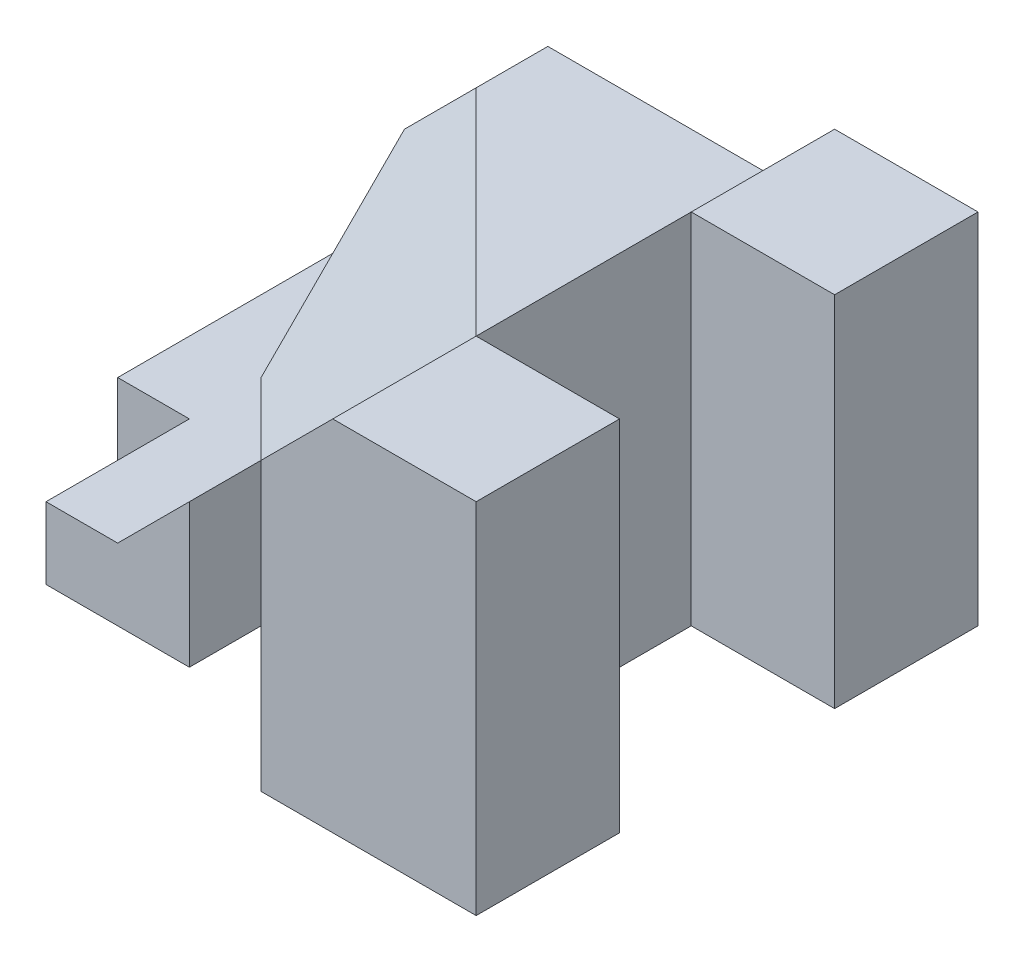
SolidWorks part; units mm, degrees
ref_plane "Front Plane" through (0, 0, 0) normal (0, 0, 1) x (1, 0, 0)
ref_plane "Top Plane" through (0, 0, 0) normal (0, 1, 0) x (1, 0, 0)
ref_plane "Right Plane" through (0, 0, 0) normal (1, 0, 0) x (0, 0, -1)
sketch "Sketch1" plane through (0, 0, 0) normal (0, 1, 0) x (1, 0, 0)
  line L0 (0, 0) -> (0, -2)
  line L1 (0, -2) -> (-2, -2)
  line L2 (-2, -2) -> (-2, -5)
  line L3 (-2, -5) -> (0, -5)
  line L4 (0, -5) -> (0, -7)
  line L5 (0, -7) -> (-3, -7)
  line L6 (-3, -7) -> (-3, -5)
  line L7 (-3, -5) -> (-5, -5)
  line L8 (-5, -5) -> (-5, -6)
  line L9 (-5, -6) -> (-7, -6)
  line L10 (-7, -6) -> (-7, -4)
  line L11 (-7, -4) -> (-8, -4)
  line L12 (-8, -4) -> (-8, 0)
  line L13 (-8, 0) -> (0, 0)
  dimension "D1" = 2
  dimension "D2" = 2
  dimension "D3" = 3
  dimension "D4" = 2
  dimension "D5" = 3
  dimension "D6" = 2
  dimension "D7" = 2
  dimension "D8" = 1
  dimension "D9" = 2
  dimension "D10" = 1
  dimension "D11" = 4
extrude "Boss-Extrude1" add sketch "Sketch1" along normal blind 5
sketch "Sketch2" plane through (0, 0, 6) normal (0, 0, 1) x (1, 0, 0)
  line L0 (-8, 1) -> (-6, 1)
  line L1 (-8, 5) -> (-8, 0) construction
  line L2 (-6, 1) -> (-2, 5)
  line L3 (-5, 5) -> (-3, 5) construction
  line L4 (-2, 5) -> (-8, 5)
  line L5 (-8, 5) -> (-8, 1)
  dimension "D1" = 4
  dimension "D2" = 2
  dimension "D3" = 6
extrude "Cut-Extrude1" cut sketch "Sketch2" against normal blind 2 and the other way blind 5
sketch "Sketch3" plane through (0, 0, 4) normal (0, 0, 1) x (1, 0, 0)
  line L0 (-2, 5) -> (-3, 5)
  line L1 (-8, 5) -> (-2, 5) construction
  line L2 (-3, 4) -> (-8, 4)
  line L3 (-6, 1) -> (-2, 5) construction
  line L4 (-3, 4) -> (-2, 5)
  line L5 (-8, 5) -> (-8, 0) construction
  line L6 (-8, 4) -> (-8, 5)
  line L7 (-8, 5) -> (-3, 5)
  dimension "D1" = 1
extrude "Cut-Extrude3" cut sketch "Sketch3" against normal blind 5
sketch "Sketch5" plane through (-8, 0, 0) normal (-1, 0, 0) x (0, 0, 1)
  line L0 (0, 4) -> (0, 0) construction
  line L1 (0, 1) -> (4, 1)
  line L2 (0, 1) -> (0, 4)
  line L3 (0, 4) -> (4, 4)
  line L4 (4, 1) -> (4, 4)
  dimension "D1" = 3
extrude "Cut-Extrude4" cut sketch "Sketch5" against normal blind 1
sketch "Sketch6" plane through (-7, 0, 0) normal (-1, 0, 0) x (0, 0, 1)
  line L0 (0, 1) -> (4, 1) construction
  point P0 (3, 1)
  dimension "D1" = 3
sketch "Sketch7" plane through (0, 0, 0) normal (0, 0, -1) x (-1, 0, 0)
  line L0 (6, 4) -> (7, 3)
  line L1 (7, 4) -> (3, 4) construction
  line L2 (7, 4) -> (7, 1) construction
  line L3 (7, 3) -> (7, 4)
  line L4 (7, 4) -> (6, 4)
  dimension "D1" = 1
  dimension "D2" = 1
extrude "Cut-Extrude5" cut sketch "Sketch7" against normal blind 1
sketch3d "3DSketch1"
  line L0 (-7, 1, 3) -> (-7, 3, 1)
  line L1 (-7, 1, 3) -> (-6, 1, 4)
  line L2 (-7, 3, 1) -> (-6, 4, 1)
  line L3 (-3, 4, 4) -> (-6, 1, 4)
  line L4 (-6, 4, 1) -> (-3, 4, 4)
extrude "Cut-Extrude6" cut sketch "3DSketch1" along direction (1, 0, 0) on the side of the normal blind 1
